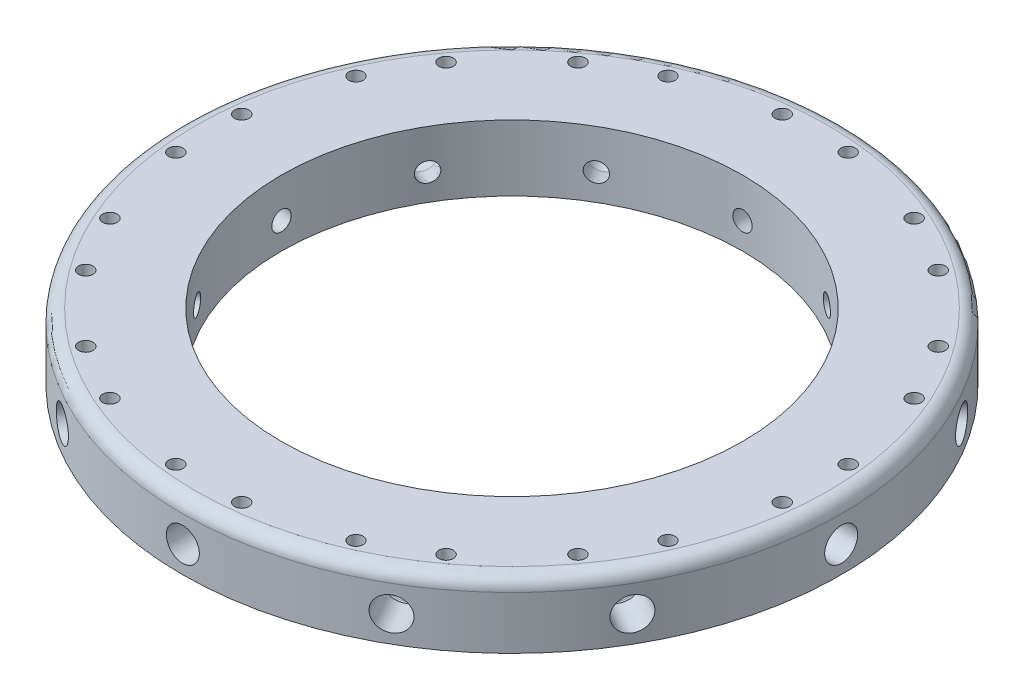
SolidWorks part; units mm, degrees
ref_plane "XY" through (0, 0, 0) normal (0, 0, 1) x (1, 0, 0)
ref_plane "XZ" through (0, 0, 0) normal (0, 1, 0) x (1, 0, 0)
ref_plane "ZY" through (0, 0, 0) normal (1, 0, 0) x (0, 0, -1)
sketch "Sketch1" plane through (0, 0, 0) normal (0, 0, 1) x (1, 0, 0)
  line L0 (0, 77.7027) -> (0, 24.0991) construction
  line L1 (175, 50) -> (240, 50)
  line L2 (175, 50) -> (175, 0)
  line L3 (175, 0) -> (250, 0)
  line L4 (250, 40) -> (250, 0)
  arc A0 (240, 50) -> (250, 40) centre (240, 40) cw
  dimension "D4" = 10
  dimension "D1" = 350
  dimension "D2" = 500
  dimension "D3" = 50
revolve "Revolve1" add sketch "Sketch1" angle 360 about L0
hole_wizard "HoleWzd1" positions "Sketch3" profile "Sketch2" legacy end condition through all
sketch "Sketch3" plane through (0, 50, 0) normal (0, 1, 0) x (1, 0, 0)
  line L0 (0, 0) -> (0, -82.5999) construction
  point P0 (-25, -230)
  point P2 (25, -230)
  dimension "D1" = 25
  dimension "D2" = 230
sketch "Sketch2" plane through (-25, 50, 230) normal (1, 0, 0) x (0, 0, 1)
  line L0 (0, 0) -> (0, 50)
  line L1 (0, 50) -> (5, 50)
  line L2 (5, 50) -> (5, 20)
  line L3 (5, 20) -> (5.5, 20)
  line L4 (5.5, 20) -> (5.5, 0)
  line L5 (5.5, 0) -> (0, 0)
  line L6 (0, 110) -> (0, -10) construction
  dimension "Průměr" = 10
  dimension "Hloubka" = 50
  dimension "Průměr válc. zahloubení" = 11
  dimension "Hloubka válc. zahloubení" = 20
sketch "Sketch4" plane through (0, 0, 0) normal (1, 0, 0) x (0, 0, -1)
  line L0 (-133.2872, 20) -> (-266.8927, 20)
  line L1 (-266.8927, 20) -> (-266.8927, 32.5)
  line L2 (-266.8927, 32.5) -> (-221.4434, 32.5)
  line L3 (-221.4434, 32.5) -> (-220.866, 31.5)
  line L5 (-218.2679, 30) -> (-190, 30)
  line L6 (-190, 30) -> (-133.2872, 20)
  line L7 (-145.4241, 20) -> (-58.7408, 20) construction
  arc A0 (-220.866, 31.5) -> (-218.2679, 30) centre (-218.2679, 33) ccw
  point P9 (-220, 30)
  dimension "D6" = 60
  dimension "D7" = 3
  dimension "D1" = 20
  dimension "D2" = 10
  dimension "D3" = 20
  dimension "D4" = 25
  dimension "D5" = 220
  dimension "D8" = 190
revolve "Cut-Revolve1" cut sketch "Sketch4" angle 360 about L7
pattern_circular "CirPattern1" count 12 over 360 about axis through (0, 0, 0) along (0, 1, 0) of "Cut-Revolve1", "HoleWzd1"
